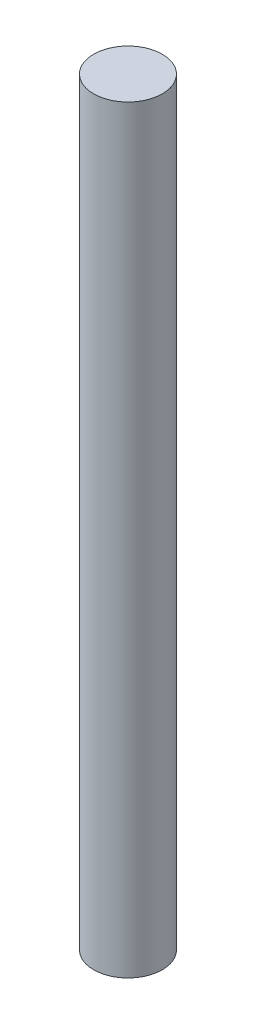
SolidWorks part; units mm, degrees
ref_plane "Front Plane" through (0, 0, 0) normal (0, 0, 1) x (1, 0, 0)
ref_plane "Top Plane" through (0, 0, 0) normal (0, 1, 0) x (1, 0, 0)
ref_plane "Right Plane" through (0, 0, 0) normal (1, 0, 0) x (0, 0, -1)
sketch "Sketch1" plane through (0, 0, 0) normal (0, 1, 0) x (1, 0, 0)
  circle A0 centre (0, 0) radius 0.95
  dimension "D1" = 1.9
extrude "Boss-Extrude1" add sketch "Sketch1" along normal blind 21
